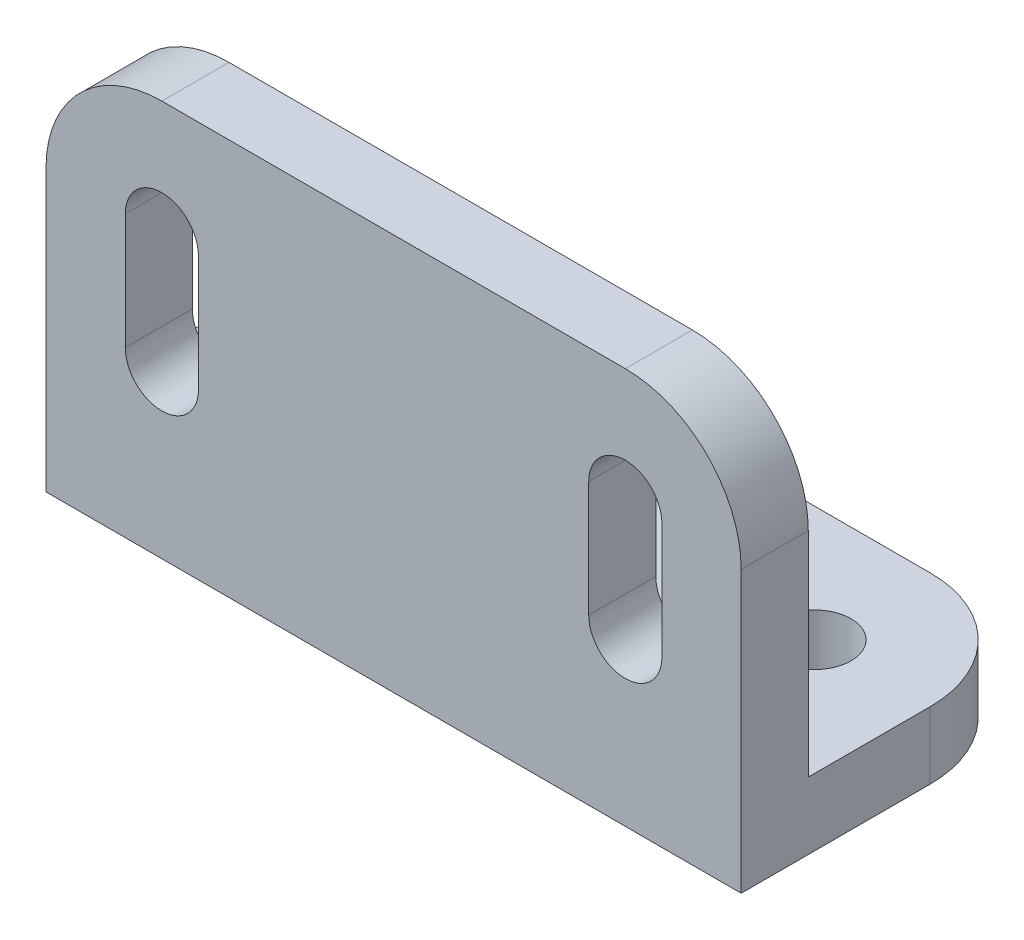
SolidWorks part; units mm, degrees
ref_plane "정면" through (0, 0, 0) normal (0, 0, 1) x (1, 0, 0)
ref_plane "윗면" through (0, 0, 0) normal (0, 1, 0) x (1, 0, 0)
ref_plane "우측면" through (0, 0, 0) normal (1, 0, 0) x (0, 0, -1)
sketch "스케치2" plane through (0, 0, 0) normal (0, 1, 0) x (1, 0, 0)
  line L1 (-57, 50) -> (57, 50)
  line L2 (-57, 50) -> (-57, 0)
  line L3 (-57, 0) -> (57, 0)
  line L4 (57, 50) -> (57, 0)
  line L5 (-57, 50) -> (57, 0) construction
  line L6 (-57, 0) -> (57, 50) construction
  point P0 (0, 25)
  point P5 (-3.8342, 30.7684)
  dimension "D1" = 0
  dimension "D2" = 0
  dimension "D3" = 50
  dimension "D4" = 114
extrude "보스-돌출1" add sketch "스케치2" along normal blind 11
fillet "필렛1" radius 19 2 edges at (57, 5.5, -50) (-57, 5.5, -50)
sketch "스케치3" plane through (0, 0, 0) normal (0, 1, 0) x (1, 0, 0)
  line L0 (57, 0) -> (57, 31) construction
  line L1 (-57, 11) -> (57, 11)
  line L2 (-57, 11) -> (-57, 0)
  line L3 (-57, 0) -> (57, 0)
  line L4 (57, 11) -> (57, 0)
  line L5 (-57, 11) -> (57, 0) construction
  line L6 (-57, 0) -> (57, 11) construction
  line L8 (-57, 0) -> (57, 0) construction
  line L9 (-57, 0) -> (57, 0) construction
  line L10 (-57, 0) -> (57, 0) construction
  point P0 (0, 5.5)
  dimension "D1" = 11
extrude "보스-돌출2" add sketch "스케치3" along normal blind 65
fillet "필렛2" radius 19 2 edges at (-57, 65, -5.5) (57, 65, -5.5)
sketch "스케치4" plane through (0, 0, 0) normal (0, 1, 0) x (1, 0, 0)
  circle A0 centre (-38, 31) radius 6
  arc A1 (-38, 50) -> (-57, 31) centre (-38, 31) ccw construction
  circle A2 centre (38, 31) radius 6
  arc A3 (57, 31) -> (38, 50) centre (38, 31) ccw construction
  dimension "D1" = 12
  dimension "D2" = 12
extrude "컷-돌출1" cut sketch "스케치4" along normal through all
sketch "스케치5" plane through (0, 0, 0) normal (0, 0, 1) x (1, 0, 0)
  line L0 (-38, 46) -> (-38, 27) construction
  line L1 (38, 46) -> (38, 27) construction
  line L2 (-44, 46) -> (-44, 27)
  line L3 (-32, 46) -> (-32, 27)
  line L4 (32, 46) -> (32, 27)
  line L5 (44, 46) -> (44, 27)
  arc A0 (-32, 46) -> (-44, 46) centre (-38, 46) ccw
  arc A1 (44, 46) -> (32, 46) centre (38, 46) ccw
  arc A2 (-38, 65) -> (-57, 46) centre (-38, 46) ccw construction
  arc A3 (57, 46) -> (38, 65) centre (38, 46) ccw construction
  arc A4 (-44, 27) -> (-32, 27) centre (-38, 27) ccw
  arc A5 (32, 27) -> (44, 27) centre (38, 27) ccw
  point P1 (26.4029, 21.0797)
  point P11 (61.2597, 11.3148)
  point P22 (-32, 46)
  point P23 (-17.848, 7.9775)
  point P24 (-65.189, 6.7414)
  dimension "D1" = 12
  dimension "D2" = 12
  dimension "D3" = 12
  dimension "D4" = 12
  dimension "D5" = 19
  dimension "D6" = 19
extrude "컷-돌출3" cut sketch "스케치5" against normal blind 65
sketch "스케치9" plane through (0, 0, 0) normal (1, 0, 0) x (0, 0, -1)
  line L0 (0, 65) -> (11, 65)
  line L1 (11, 65) -> (50, 11)
  line L2 (50, 11) -> (50, 0)
  line L3 (50, 0) -> (0, 0)
  line L4 (0, 0) -> (0, 65)
extrude "보스-돌출3" add sketch "스케치9" along normal mid plane 6
